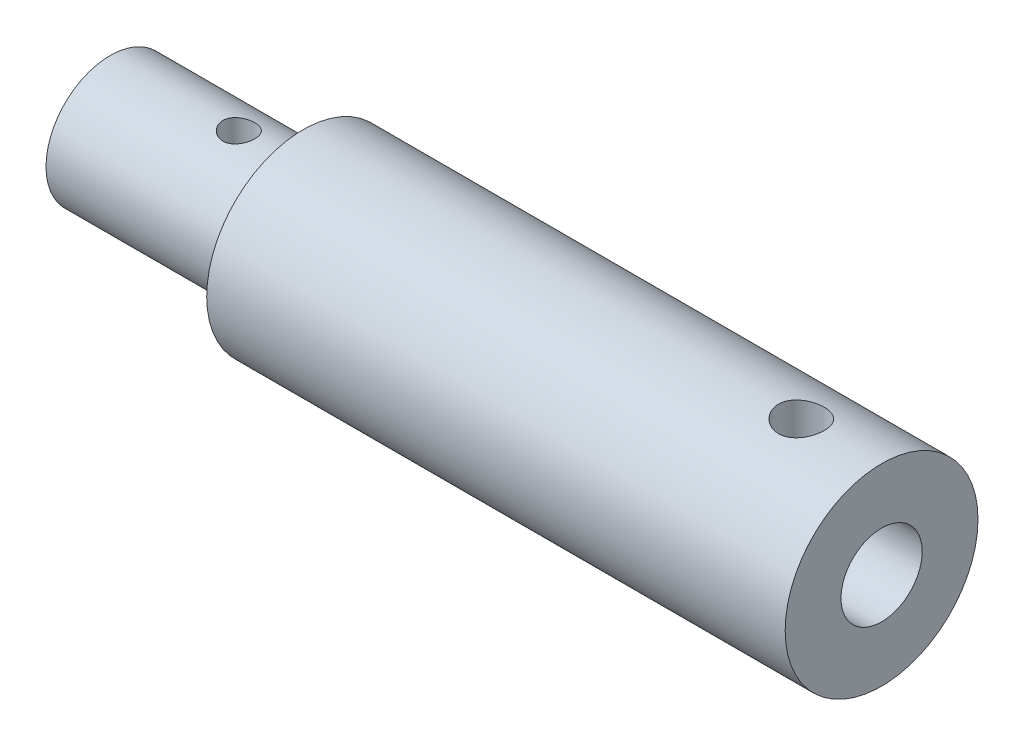
SolidWorks part; units mm, degrees
ref_plane "Front Plane" through (0, 0, 0) normal (0, 0, 1) x (1, 0, 0)
ref_plane "Top Plane" through (0, 0, 0) normal (0, 1, 0) x (1, 0, 0)
ref_plane "Right Plane" through (0, 0, 0) normal (1, 0, 0) x (0, 0, -1)
sketch "Sketch1" plane through (0, 0, 0) normal (1, 0, 0) x (0, 0, -1)
  circle A0 centre (0, 0) radius 4.7625
  dimension "D1" = 9.525
extrude "Boss-Extrude1" add sketch "Sketch1" along normal blind 38.1
sketch "Sketch2" plane through (38.1, 0, 0) normal (1, 0, 0) x (0, 0, -1)
  circle A0 centre (0, 0) radius 2.0066
extrude "Cut-Extrude1" cut sketch "Sketch2" against normal blind 7.9248
sketch "Sketch3" plane through (0, 0, 0) normal (0, 1, 0) x (1, 0, 0)
  line L0 (38.1, -4.7625) -> (38.1, 4.7625) construction
  circle A0 centre (34.1376, 0) radius 1.1303
  dimension "D1" = 3.9624
extrude "Cut-Extrude2" cut sketch "Sketch3" along normal blind 8.6868
sketch "Sketch4" plane through (0, 0, 0) normal (-1, 0, 0) x (0, 0, 1)
  circle A0 centre (0, 0) radius 3.175
  circle A1 centre (0, 0) radius 5.0848
extrude "Cut-Extrude3" cut sketch "Sketch4" against normal blind 9.525
sketch "Sketch5" plane through (0, 0, 0) normal (0, 1, 0) x (1, 0, 0)
  line L0 (9.525, 4.7625) -> (9.525, -4.7625) construction
  circle A0 centre (6.35, 0) radius 0.7874
  dimension "D1" = 3.175
extrude "Cut-Extrude4" cut sketch "Sketch5" against normal through all and the other way through all
